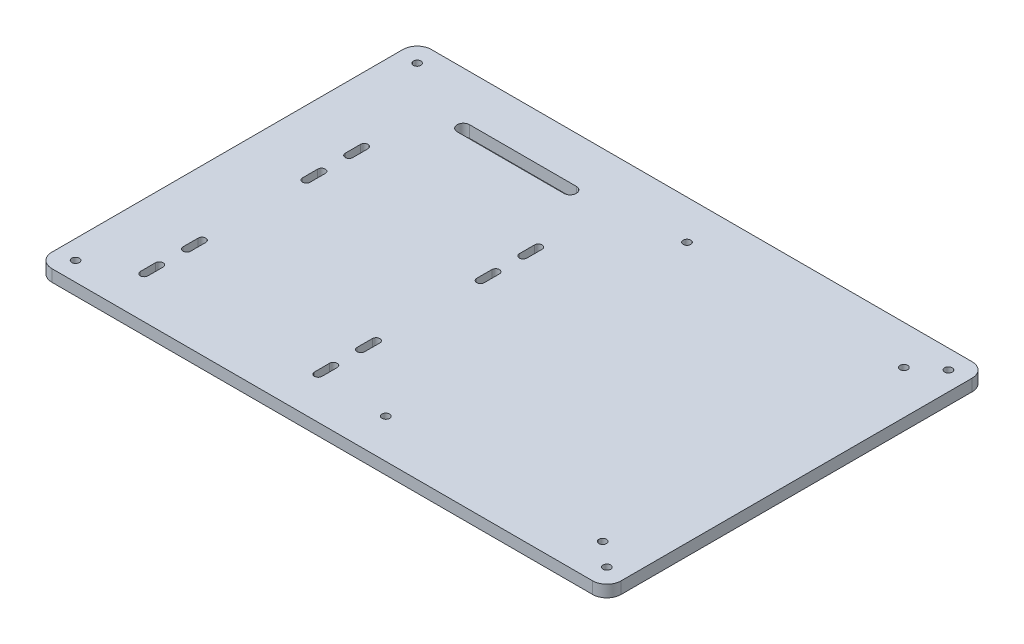
SolidWorks part; units mm, degrees
ref_plane "Front Plane" through (0, 0, 0) normal (0, 0, 1) x (1, 0, 0)
ref_plane "Top Plane" through (0, 0, 0) normal (0, 1, 0) x (1, 0, 0)
ref_plane "Right Plane" through (0, 0, 0) normal (1, 0, 0) x (0, 0, -1)
sketch "Sketch1" plane through (0, 0, 0) normal (0, 1, 0) x (1, 0, 0)
  line L1 (-120, 80) -> (120, 80)
  line L2 (-120, 80) -> (-120, -80)
  line L3 (-120, -80) -> (120, -80)
  line L4 (120, 80) -> (120, -80)
  line L5 (-120, 80) -> (120, -80) construction
  line L6 (-120, -80) -> (120, 80) construction
  point P0 (0, 0)
  dimension "D1" = 160
  dimension "D2" = 240
extrude "Boss-Extrude1" add sketch "Sketch1" along normal blind 5
sketch "Sketch2" plane through (0, 5, 0) normal (0, 1, 0) x (1, 0, 0)
  line L0 (0, 80) -> (0, -80) construction
  line L1 (120, 80) -> (-120, 80) construction
  line L2 (-120, -80) -> (120, -80) construction
  line L3 (-120, 0) -> (120, 0) construction
  line L4 (-120, 80) -> (-120, -80) construction
  line L5 (120, -80) -> (120, 80) construction
  line L6 (-56, 0) -> (-56, 80) construction
  line L7 (-56, 0) -> (-56, -80) construction
  line L8 (56, 80) -> (56, -80) construction
  line L9 (-94.3, 30.4) -> (-94.3, 24)
  line L10 (-91.1, 30.4) -> (-91.1, 24)
  line L11 (-94.3, 12.4) -> (-94.3, 6)
  line L12 (-91.1, 12.4) -> (-91.1, 6)
  line L13 (-20.9, 12.4) -> (-20.9, 6)
  line L14 (-17.7, 12.4) -> (-17.7, 6)
  line L15 (-20.9, 30.4) -> (-20.9, 24)
  line L16 (-17.7, 30.4) -> (-17.7, 24)
  line L17 (-94.3, -62.4) -> (-94.3, -56)
  line L18 (-91.1, -62.4) -> (-91.1, -56)
  line L19 (-91.1, -44.4) -> (-91.1, -38)
  line L20 (-94.3, -44.4) -> (-94.3, -38)
  line L21 (-78.5, 55.4) -> (-33.5, 55.4)
  line L22 (-78.5, 60.6) -> (-33.5, 60.6)
  line L23 (-17.7, -62.4) -> (-17.7, -56)
  line L24 (-20.9, -62.4) -> (-20.9, -56)
  line L25 (-120, -16) -> (120, -16) construction
  line L26 (-20.9, -44.4) -> (-20.9, -38)
  line L27 (-17.7, -44.4) -> (-17.7, -38)
  circle A0 centre (-112, 72) radius 1.6
  circle A1 centre (-112, -72) radius 1.6
  circle A2 centre (112, 72) radius 1.6
  circle A3 centre (112, -72) radius 1.6
  arc A4 (-94.3, 24) -> (-91.1, 24) centre (-92.7, 24) ccw
  arc A5 (-94.3, 6) -> (-91.1, 6) centre (-92.7, 6) ccw
  arc A6 (-17.7, 6) -> (-20.9, 6) centre (-19.3, 6) cw
  arc A7 (-17.7, 24) -> (-20.9, 24) centre (-19.3, 24) cw
  arc A8 (-91.1, -62.4) -> (-94.3, -62.4) centre (-92.7, -62.4) cw
  arc A9 (-94.3, -56) -> (-91.1, -56) centre (-92.7, -56) cw
  arc A10 (-91.1, -44.4) -> (-94.3, -44.4) centre (-92.7, -44.4) cw
  arc A11 (-94.3, -38) -> (-91.1, -38) centre (-92.7, -38) cw
  circle A12 centre (10.28, 63.5) radius 1.6
  circle A13 centre (101.72, 63.5) radius 1.6
  circle A14 centre (101.72, -63.5) radius 1.6
  circle A15 centre (10.28, -63.5) radius 1.6
  arc A16 (-91.1, 30.4) -> (-94.3, 30.4) centre (-92.7, 30.4) ccw
  arc A17 (-91.1, 12.4) -> (-94.3, 12.4) centre (-92.7, 12.4) ccw
  arc A18 (-20.9, 12.4) -> (-17.7, 12.4) centre (-19.3, 12.4) cw
  arc A19 (-20.9, 30.4) -> (-17.7, 30.4) centre (-19.3, 30.4) cw
  arc A20 (-33.5, 55.4) -> (-33.5, 60.6) centre (-33.5, 58) ccw
  arc A21 (-20.9, -62.4) -> (-17.7, -62.4) centre (-19.3, -62.4) ccw
  arc A22 (-17.7, -56) -> (-20.9, -56) centre (-19.3, -56) ccw
  arc A23 (-17.7, -38) -> (-20.9, -38) centre (-19.3, -38) ccw
  arc A24 (-20.9, -44.4) -> (-17.7, -44.4) centre (-19.3, -44.4) ccw
  arc A27 (-78.5, 55.4) -> (-78.5, 60.6) centre (-78.5, 58) cw
  point P31 (-56, -64.6604)
  point P78 (-56, 55.4)
  point P79 (-56, 60.6)
  dimension "D1" = 8
  dimension "D3" = 56
  dimension "D4" = 36.7
  dimension "D5" = 18
  dimension "D10" = 45.72
  dimension "D15" = 22.5
  dimension "D2" = 8
  dimension "D6" = 16
  dimension "D7" = 36.7
  dimension "D8" = 22
  dimension "D9" = 56
  dimension "D11" = 63.5
  dimension "D12" = 6.4
  dimension "D13" = 22
  dimension "D14" = 6.4
extrude "Cut-Extrude1" cut sketch "Sketch2" against normal blind 5
fillet "Fillet1" radius 6 4 edges at (-120, 2.5, 80) (120, 2.5, 80) (120, 2.5, -80) (-120, 2.5, -80)
